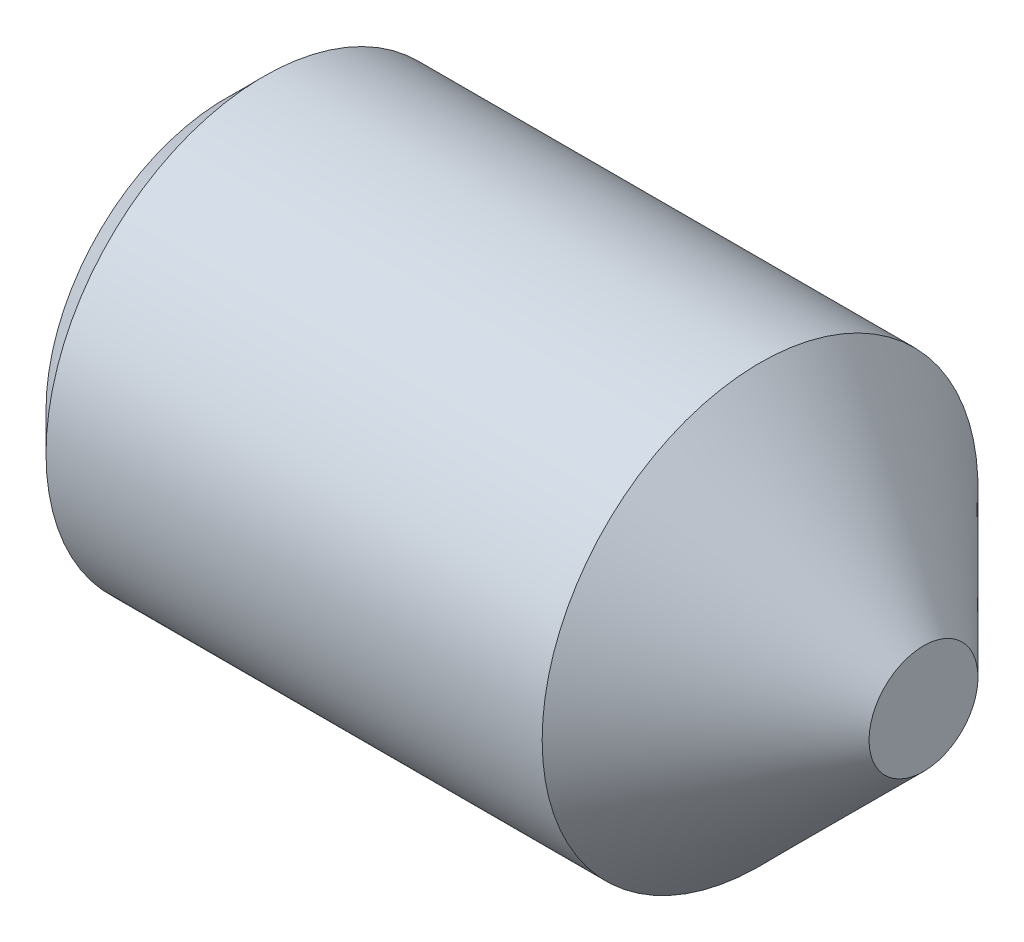
SolidWorks part; units mm, degrees
ref_plane "Front" through (0, 0, 0) normal (0, 0, 1) x (1, 0, 0)
ref_plane "Top" through (0, 0, 0) normal (0, 1, 0) x (1, 0, 0)
ref_plane "Right" through (0, 0, 0) normal (1, 0, 0) x (0, 0, -1)
sketch "Sketch1" plane through (0, 0, 0) normal (0, 0, 1) x (1, 0, 0)
  line L0 (0, 0) -> (8, 0)
  line L1 (8, 0) -> (8, 0.625)
  line L2 (8, 0.625) -> (6.125, 2.5)
  line L3 (6.125, 2.5) -> (0.433, 2.5)
  line L4 (0.433, 2.5) -> (0, 2.067)
  line L5 (0, 2.067) -> (0, 0)
  line L6 (-14.7741, 0) -> (12.5137, 0) construction
  dimension "D1" = 45
  dimension "l" = 8
  dimension "D2" = 45
  dimension "dt" = 1.25
  dimension "d" = 5
  dimension "df" = 4.134
revolve "Base" add sketch "Sketch1" angle 360 about L6
cosmetic thread "ThreadCosmetic1" [suppressed] parameters "D2"=4.134
sketch "Sketch2" plane through (0, 0.2203, -0.1392) normal (-1, 0, 0) x (0, 0, 1)
  line L1 (1.5826, -0.2203) -> (0.8609, 1.0297)
  line L2 (0.8609, 1.0297) -> (-0.5825, 1.0297)
  line L3 (-0.5825, 1.0297) -> (-1.3042, -0.2203)
  line L4 (-1.3042, -0.2203) -> (-0.5825, -1.4703)
  line L5 (-0.5825, -1.4703) -> (0.8609, -1.4703)
  line L6 (0.8609, -1.4703) -> (1.5826, -0.2203)
  circle A0 centre (0.1392, -0.2203) radius 1.25 construction
  dimension "s" = 2.5
extrude "HexagonSocket" cut sketch "Sketch2" against normal blind 2
sketch "Sketch3" plane through (0, 0, 0) normal (0, 0, 1) x (1, 0, 0)
  line L0 (2, 0) -> (-2.4777, 0) construction
  line L2 (2, 1.25) -> (2.7217, 0)
  line L3 (2.7217, 0) -> (2, -1.25) construction
  line L4 (2, 1.25) -> (2, 0)
  line L5 (2, 0) -> (2.7217, 0)
  dimension "D1" = 120
revolve "Cut-Revolve" cut sketch "Sketch3" angle 360 about L0
sketch "Sketch4" plane through (0, 0, 0) normal (0, 0, 1) x (1, 0, 0)
  line L0 (0.433, 2.125) -> (0.6495, 2.5)
  line L1 (0.6495, 2.5) -> (0.6495, 2.933)
  line L2 (0.6495, 2.933) -> (0.2165, 2.933)
  line L3 (0.2165, 2.933) -> (0.2165, 2.5)
  line L4 (0.2165, 2.5) -> (0.433, 2.125)
  line L5 (0, 0) -> (3.2295, 0) construction
  line L6 (0.433, 2.5) -> (0.433, -2.5) construction
  dimension "D1" = 5
  dimension "D2" = 0.433
revolve "Cut-Revolve10" [suppressed] cut sketch "Sketch4" angle 360 about L5
pattern_linear "LPattern10" [suppressed] count 15 spacing 0.5196 along (1, 0, 0)
equation "\"df@Sketch1\" = \"D2@ThreadCosmetic1\""
equation "\"D1@Sketch4\" = \"d@Sketch1\""
equation "\"D2@Sketch4\" =  ( \"d@Sketch1\" - \"D2@ThreadCosmetic1\" )  / 2"
equation "\"D3@LPattern10\" = \"D2@Sketch4\" * 1.2"
equation "\"D1@LPattern10\" = \"l@Sketch1\" / \"D3@LPattern10\""
